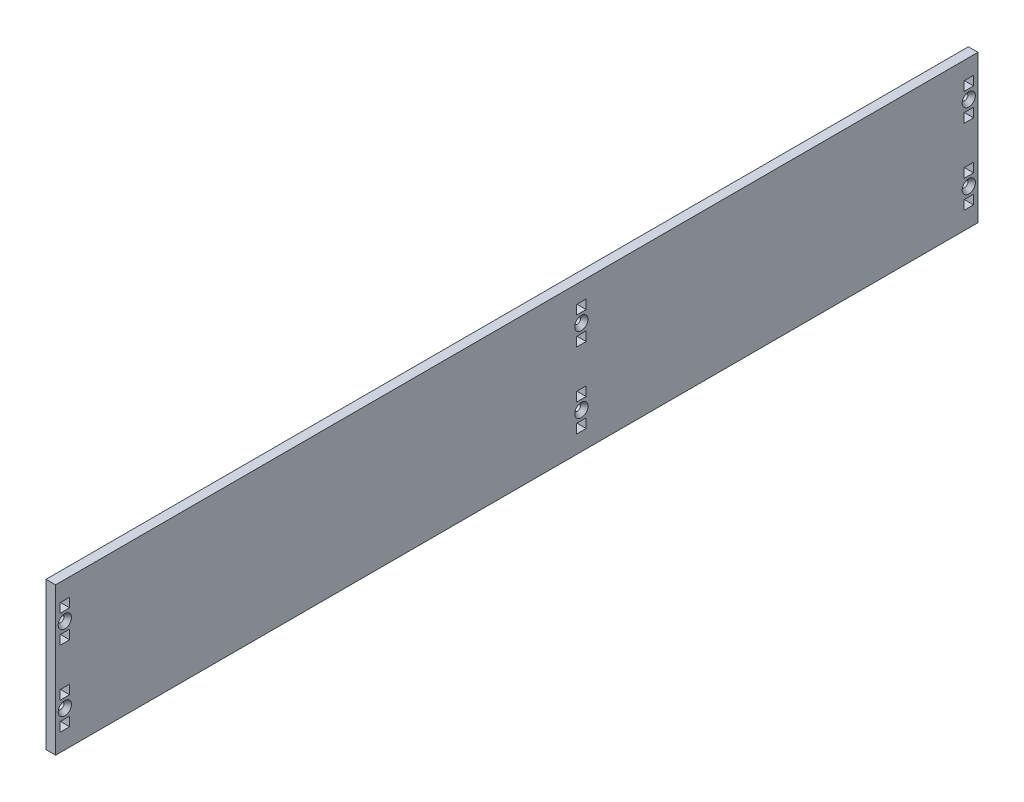
SolidWorks part; units mm, degrees
material "Acrylic (Blue)"
ref_plane "Front Plane" through (0, 0, 0) normal (0, 0, 1) x (1, 0, 0)
ref_plane "Top Plane" through (0, 0, 0) normal (0, 1, 0) x (1, 0, 0)
ref_plane "Right Plane" through (0, 0, 0) normal (1, 0, 0) x (0, 0, -1)
sketch "Sketch1" plane through (0, 0, 0) normal (1, 0, 0) x (0, 0, -1)
  line L0 (0, 0) -> (266.7, 0) construction
  line L1 (266.7, 0) -> (273.05, 0) construction
  line L2 (0, 0) -> (-355.6, 0) construction
  line L3 (-355.6, 0) -> (-361.95, 0) construction
  line L4 (-355.6, 25.9207) -> (-355.6, -25.9207) construction
  line L5 (266.7, 25.9207) -> (266.7, -25.9207) construction
  line L6 (0, 25.9207) -> (0, -25.9207) construction
  line L7 (-361.95, 50.8) -> (273.05, 50.8)
  line L8 (-361.95, 50.8) -> (-361.95, -50.8)
  line L9 (-361.95, -50.8) -> (273.05, -50.8)
  line L10 (273.05, 50.8) -> (273.05, -50.8)
  line B0 (-352.298, 19.5707) -> (-352.298, 13.2207)
  line B1 (-352.298, 13.2207) -> (-358.902, 13.2207)
  line B2 (-358.902, 13.2207) -> (-358.902, 19.5707)
  line B3 (-358.902, 19.5707) -> (-352.298, 19.5707)
  line B4 (-352.298, 38.6207) -> (-352.298, 32.2707)
  line B5 (-352.298, 32.2707) -> (-358.902, 32.2707)
  line B6 (-358.902, 32.2707) -> (-358.902, 38.6207)
  line B7 (-358.902, 38.6207) -> (-352.298, 38.6207)
  circle B8 centre (-355.6, 25.9207) radius 2.1526
  line B9 (-352.298, -32.2707) -> (-352.298, -38.6207)
  line B10 (-352.298, -38.6207) -> (-358.902, -38.6207)
  line B11 (-358.902, -38.6207) -> (-358.902, -32.2707)
  line B12 (-358.902, -32.2707) -> (-352.298, -32.2707)
  line B13 (-352.298, -13.2207) -> (-352.298, -19.5707)
  line B14 (-352.298, -19.5707) -> (-358.902, -19.5707)
  line B15 (-358.902, -19.5707) -> (-358.902, -13.2207)
  line B16 (-358.902, -13.2207) -> (-352.298, -13.2207)
  circle B17 centre (-355.6, -25.9207) radius 2.1526
  line B18 (-3.302, -19.5707) -> (-3.302, -13.2207)
  line B19 (-3.302, -13.2207) -> (3.302, -13.2207)
  line B20 (3.302, -13.2207) -> (3.302, -19.5707)
  line B21 (3.302, -19.5707) -> (-3.302, -19.5707)
  line B22 (-3.302, -38.6207) -> (-3.302, -32.2707)
  line B23 (-3.302, -32.2707) -> (3.302, -32.2707)
  line B24 (3.302, -32.2707) -> (3.302, -38.6207)
  line B25 (3.302, -38.6207) -> (-3.302, -38.6207)
  circle B26 centre (0, -25.9207) radius 2.1526
  line B27 (-3.302, 32.2707) -> (-3.302, 38.6207)
  line B28 (-3.302, 38.6207) -> (3.302, 38.6207)
  line B29 (3.302, 38.6207) -> (3.302, 32.2707)
  line B30 (3.302, 32.2707) -> (-3.302, 32.2707)
  line B31 (-3.302, 13.2207) -> (-3.302, 19.5707)
  line B32 (-3.302, 19.5707) -> (3.302, 19.5707)
  line B33 (3.302, 19.5707) -> (3.302, 13.2207)
  line B34 (3.302, 13.2207) -> (-3.302, 13.2207)
  circle B35 centre (0, 25.9207) radius 2.1526
  line B36 (263.398, -19.5707) -> (263.398, -13.2207)
  line B37 (263.398, -13.2207) -> (270.002, -13.2207)
  line B38 (270.002, -13.2207) -> (270.002, -19.5707)
  line B39 (270.002, -19.5707) -> (263.398, -19.5707)
  line B40 (263.398, -38.6207) -> (263.398, -32.2707)
  line B41 (263.398, -32.2707) -> (270.002, -32.2707)
  line B42 (270.002, -32.2707) -> (270.002, -38.6207)
  line B43 (270.002, -38.6207) -> (263.398, -38.6207)
  circle B44 centre (266.7, -25.9207) radius 2.1526
  line B45 (263.398, 32.2707) -> (263.398, 38.6207)
  line B46 (263.398, 38.6207) -> (270.002, 38.6207)
  line B47 (270.002, 38.6207) -> (270.002, 32.2707)
  line B48 (270.002, 32.2707) -> (263.398, 32.2707)
  line B49 (263.398, 13.2207) -> (263.398, 19.5707)
  line B50 (263.398, 19.5707) -> (270.002, 19.5707)
  line B51 (270.002, 19.5707) -> (270.002, 13.2207)
  line B52 (270.002, 13.2207) -> (263.398, 13.2207)
  circle B53 centre (266.7, 25.9207) radius 2.1526
  dimension "D1" = 355.6
  dimension "D2" = 101.6
  dimension "D3" = 51.8414
  dimension "D4" = 6.35
  dimension "D5" = 266.7
sketch_block_instance "BOLT_HOLE-7"
sketch_block "BOLT_HOLE" parameters "D1"=4.3053, "D2"=6.35, "D3"=6.35, "D4"=6.604
sketch_block_instance "BOLT_HOLE-8"
sketch_block_instance "BOLT_HOLE-9"
sketch_block_instance "BOLT_HOLE-10"
sketch_block_instance "BOLT_HOLE-11"
sketch_block_instance "BOLT_HOLE-12"
extrude "Boss-Extrude1" add sketch "Sketch1" along normal blind 6.604
hole_wizard "CSK for #8 Flat Head Socket Cap Screw1" positions "Sketch3" profile "Sketch2" countersink size "#8" standard "ANSI Inch" end condition through all
sketch "Sketch3" plane through (6.604, 0, 0) normal (1, 0, 0) x (0, 0, -1)
  point P0 (-355.6, 25.9207)
  point P3 (-355.6, -25.9207)
  point P6 (0, 25.9207)
  point P9 (0, -25.9207)
  point P12 (266.7, 25.9207)
  point P15 (266.7, -25.9207)
sketch "Sketch2" plane through (6.604, 25.9207, 355.6) normal (0, 1, 0) x (0, 0, -1)
  line L0 (0, 0) -> (0, 6.604)
  line L1 (0, 6.604) -> (2.1526, 6.604)
  line L2 (2.1526, 6.604) -> (2.1526, 2.7685)
  line L3 (2.1526, 2.7685) -> (4.5593, 0)
  line L5 (4.5593, 0) -> (0, 0)
  line L6 (-2.1526, 2.7685) -> (-4.5593, 0) construction
  line L11 (0, -6.35) -> (0, 107.95) construction
  dimension "Thru Hole Dia." = 4.3053
  dimension "Thru Hole Depth" = 6.604
  dimension "Near C'Sink Dia." = 9.1186
  dimension "Near C'Sink Angle" = 82
other "Move Face1" [suppressed] parameters "D1"=0.0508
